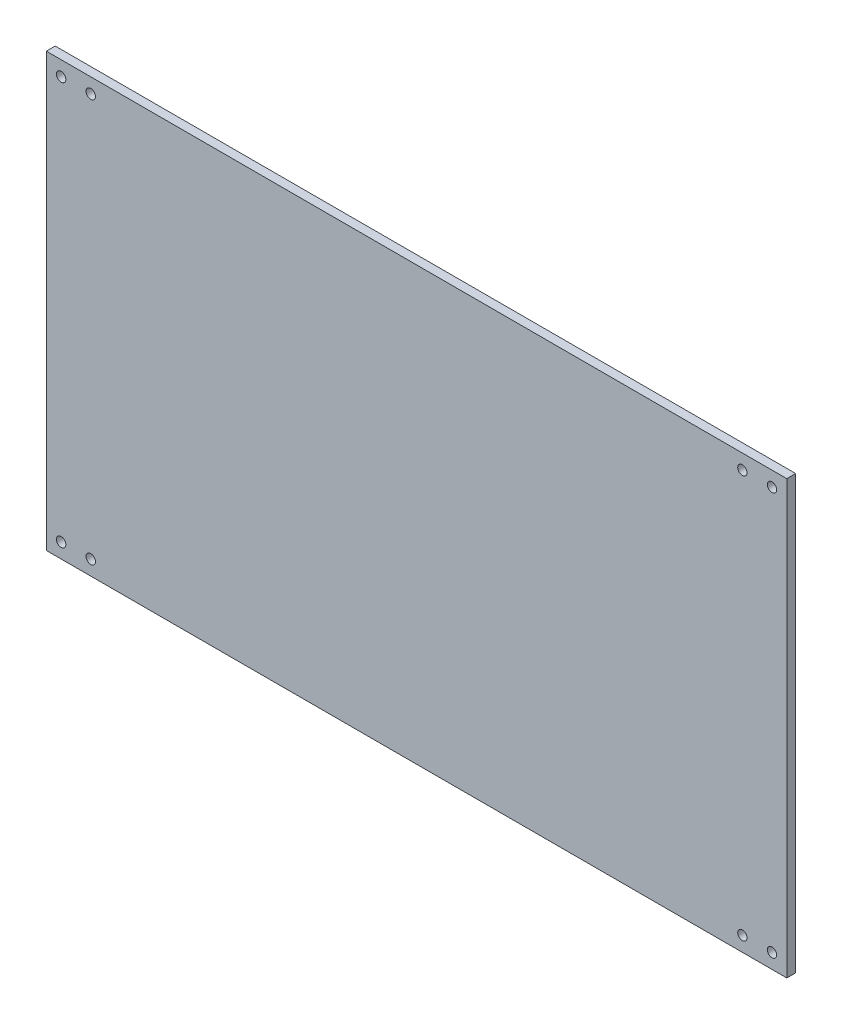
SolidWorks part; units mm, degrees
material "Thornel Mat VMA"
ref_plane "前视基准面" through (0, 0, 0) normal (0, 0, 1) x (1, 0, 0)
ref_plane "上视基准面" through (0, 0, 0) normal (0, 1, 0) x (1, 0, 0)
ref_plane "右视基准面" through (0, 0, 0) normal (1, 0, 0) x (0, 0, -1)
other "Configuration Table"
sketch "草图1" plane through (0, 0, 0) normal (0, 0, 1) x (1, 0, 0)
  line L0 (-142.9899, -71.7211) -> (-132.9899, -71.7211) construction
  line L1 (-147.9899, 69.2789) -> (102.0101, 69.2789)
  line L2 (-147.9899, 69.2789) -> (-147.9899, -76.7211)
  line L3 (-147.9899, -76.7211) -> (102.0101, -76.7211)
  line L4 (102.0101, 69.2789) -> (102.0101, -76.7211)
  line L5 (-147.9899, -3.7211) -> (102.0101, -3.7211) construction
  circle A0 centre (-142.9899, -71.7211) radius 1.6
  circle A1 centre (-132.9899, -71.7211) radius 1.6
  circle A2 centre (-142.9899, 64.2789) radius 1.6
  circle A3 centre (-132.9899, 64.2789) radius 1.6
  circle A4 centre (97.0101, -71.7211) radius 1.5703
  circle A5 centre (87.0101, -71.7211) radius 1.5703
  circle A6 centre (97.0101, 64.2789) radius 1.5703
  circle A7 centre (87.0101, 64.2789) radius 1.5703
  point P20 (86.1731, -76.7211)
  dimension "D3" = 10
  dimension "D6" = 3.2
  dimension "D7" = 10
  dimension "D1" = 250
  dimension "D2" = 146
  dimension "D4" = 5
  dimension "D5" = 5
  dimension "D8" = 5
  dimension "D9" = 5
extrude "凸台-拉伸1" add sketch "草图1" along normal blind 3
